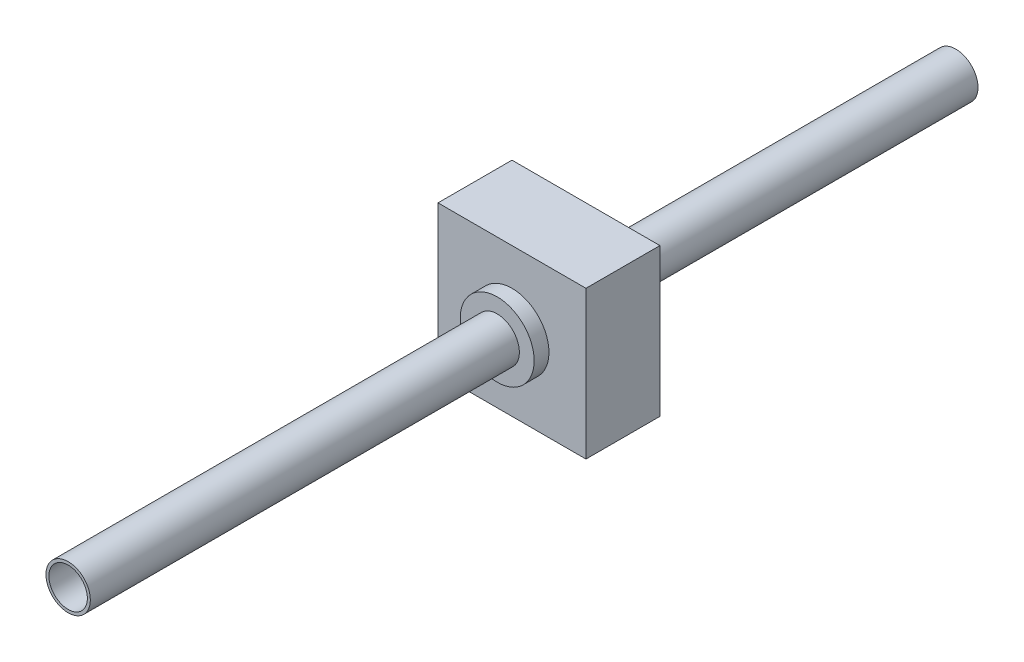
SolidWorks part; units mm, degrees
ref_plane "Front Plane" through (0, 0, 0) normal (0, 0, 1) x (1, 0, 0)
ref_plane "Top Plane" through (0, 0, 0) normal (0, 1, 0) x (1, 0, 0)
ref_plane "Right Plane" through (0, 0, 0) normal (1, 0, 0) x (0, 0, -1)
sketch "Sketch1" plane through (0, 0, 0) normal (0, 0, 1) x (1, 0, 0)
  line L1 (-500, 500) -> (500, 500)
  line L2 (-500, 500) -> (-500, -500)
  line L3 (-500, -500) -> (500, -500)
  line L4 (500, 500) -> (500, -500)
  line L5 (-500, 500) -> (500, -500) construction
  line L6 (-500, -500) -> (500, 500) construction
  circle A0 centre (0, 0) radius 250
  point P0 (0, 0)
  dimension "D3" = 500
  dimension "D1" = 1000
  dimension "D2" = 1000
ref_plane "Plane1" through (0, 0, 3000) normal (0, 0, 1) x (1, 0, 0)
sketch "Sketch4" plane through (0, 0, 3000) normal (0, 0, 1) x (1, 0, 0)
  circle A0 centre (0, 0) radius 150
sketch "Sketch6" plane through (0, 0, 0) normal (0, 1, 0) x (1, 0, 0)
  line L0 (0, -3000) -> (0, 3000)
  line L1 (-150, -3000) -> (150, -3000) construction
  dimension "D1" = 6000
extrude "Boss-Extrude1" add sketch "Sketch1" against normal blind 500
sweep "Sweep-Thin3" add profiles "Sketch4" path "Sketch6" parameters "D1"=20
ref_plane "Plane2" through (0, 0, 100) normal (0, 0, 1) x (1, 0, 0)
sketch "Sketch8" plane through (0, 0, 100) normal (0, 0, 1) x (1, 0, 0)
  circle A0 centre (0, 0) radius 250
  circle A1 centre (0, 0) radius 150
  dimension "D1" = 300
extrude "Boss-Extrude3" add sketch "Sketch8" against normal blind 700 separate body
